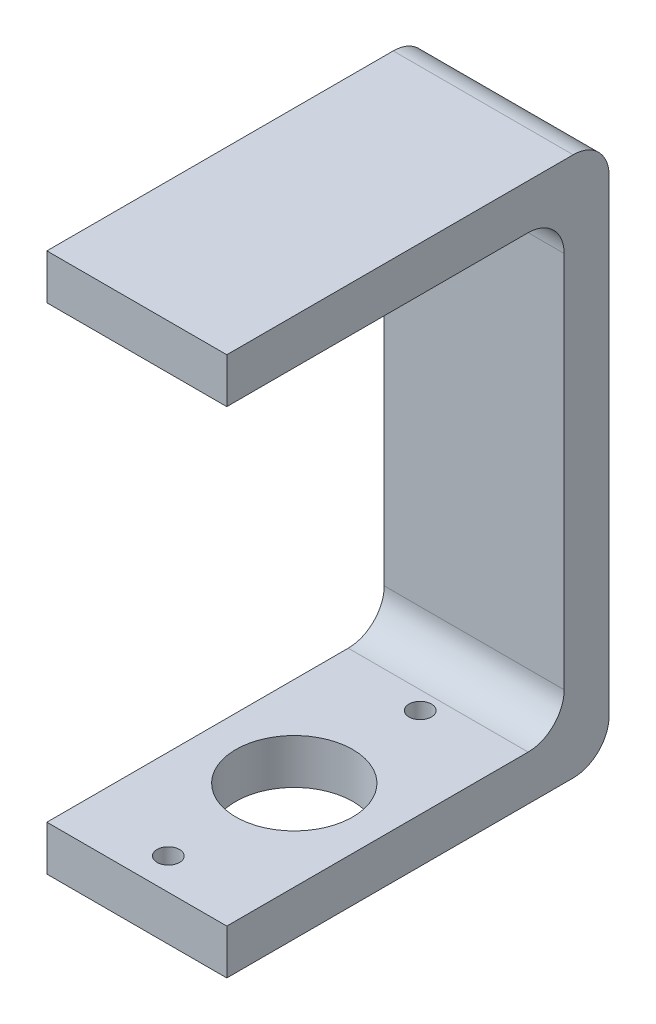
SolidWorks part; units mm, degrees
material "普通碳钢"
ref_plane "前视基准面" through (0, 0, 0) normal (0, 0, 1) x (1, 0, 0)
ref_plane "上视基准面" through (0, 0, 0) normal (0, 1, 0) x (1, 0, 0)
ref_plane "右视基准面" through (0, 0, 0) normal (1, 0, 0) x (0, 0, -1)
sketch "草图1" plane through (0, 0, 0) normal (1, 0, 0) x (0, 0, -1)
  line L0 (0, 0) -> (77, 0)
  line L1 (85, 8) -> (85, 112)
  line L2 (77, 120) -> (0, 120)
  line L3 (0, 120) -> (0, 110)
  line L4 (0, 110) -> (67, 110)
  line L5 (75, 102) -> (75, 18)
  line L6 (67, 10) -> (0, 10)
  line L7 (0, 10) -> (0, 0)
  arc A0 (67, 10) -> (75, 18) centre (67, 18) ccw
  arc A1 (75, 102) -> (67, 110) centre (67, 102) ccw
  arc A2 (85, 8) -> (77, 0) centre (77, 8) cw
  arc A3 (85, 112) -> (77, 120) centre (77, 112) ccw
  point P11 (75, 10)
  point P14 (75, 110)
  point P17 (85, 0)
  point P20 (85, 120)
  dimension "D7" = 8
  dimension "D1" = 85
  dimension "D2" = 75
  dimension "D3" = 10
  dimension "D5" = 100
  dimension "D6" = 10
extrude "凸台-拉伸1" add sketch "草图1" along normal blind 40
sketch "草图5" plane through (0, 0, 0) normal (0, -1, 0) x (1, 0, 0)
  line L0 (20, 0) -> (20, -70) construction
  line L1 (40, 0) -> (0, 0) construction
  circle A0 centre (20, -35) radius 13
  circle A1 centre (20, -35) radius 28 construction
  dimension "D1" = 26
  dimension "D3" = 56
  dimension "D2" = 35
extrude "切除-拉伸1" cut sketch "草图5" against normal up to next
hole_wizard "M6 螺纹孔1" positions "3D草图1" profile "草图6" tap size "M6" standard "Gb" end condition up to next
sketch3d "3D草图1"
  line L0 (20, 0, 0) -> (20, 0, -70) construction
  circle A0 centre (20, 0, -35) radius 28 construction
  point P0 (20, 0, -7)
  point P6 (20, -28, -35)
  point P7 (20, 0, -63)
cosmetic thread "孔螺蚊线1" parameters "D2"=6
cosmetic thread "孔螺蚊线2" parameters "D2"=6
sketch "草图6" plane through (20, 0, -7) normal (1, 0, 0) x (0, 0, -1)
  line L0 (0, 0) -> (0, 10)
  line L1 (0, 10) -> (2.5, 10)
  line L2 (2.5, 10) -> (2.5, 0)
  line L5 (2.5, 0) -> (0, 0)
  line L11 (0, -6.35) -> (0, 107.95) construction
  dimension "通孔螺纹孔钻头直径" = 5
  dimension "通孔螺纹孔钻头深度" = 10
